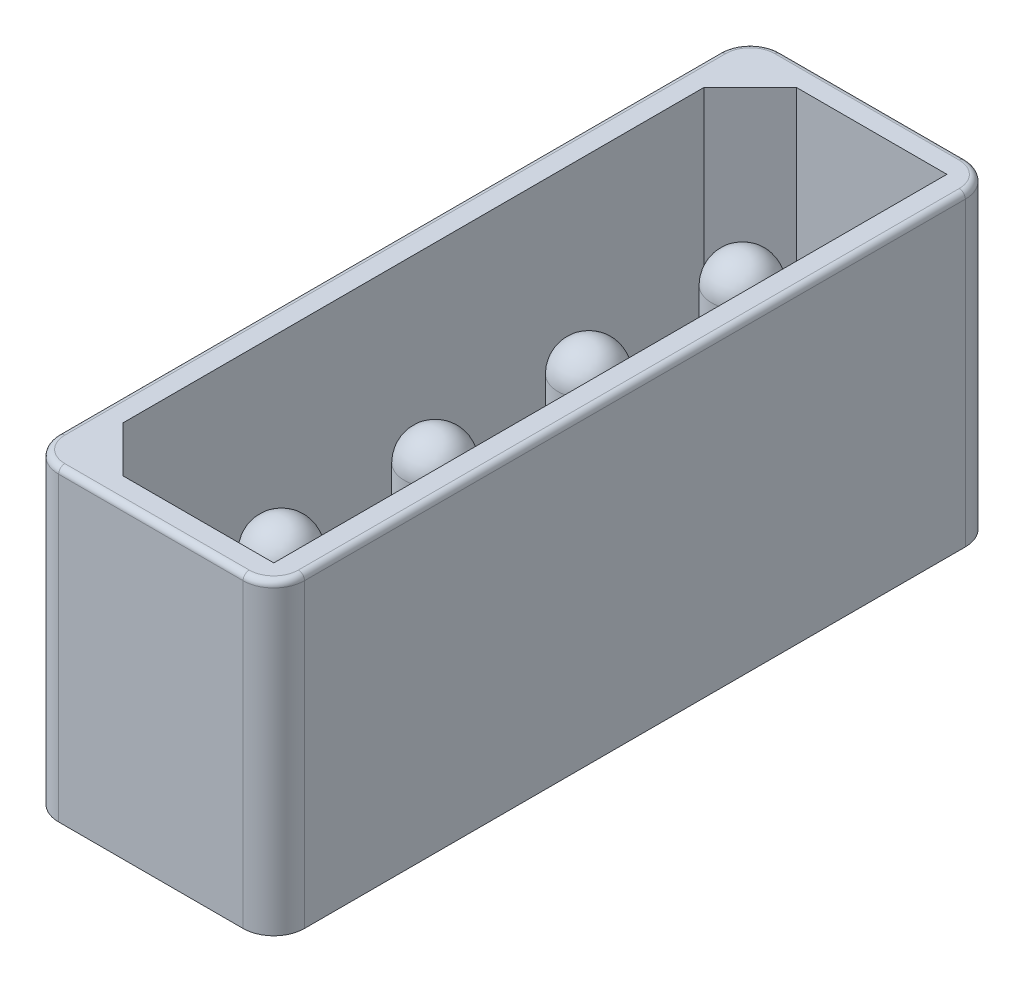
SolidWorks part; units mm, degrees
material "Duranickel(R) 301"
ref_plane "Alzado" through (0, 0, 0) normal (0, 0, 1) x (1, 0, 0)
ref_plane "Planta" through (0, 0, 0) normal (0, 1, 0) x (1, 0, 0)
ref_plane "Vista lateral" through (0, 0, 0) normal (1, 0, 0) x (0, 0, -1)
sketch "Croquis1" plane through (0, 0, 0) normal (0, 1, 0) x (1, 0, 0)
  line L0 (-3.2, 10.95) -> (-3.2, -10.95)
  line L1 (-4, 11.75) -> (4, 11.75)
  line L2 (-4, 11.75) -> (-4, -11.75)
  line L3 (-4, -11.75) -> (4, -11.75)
  line L4 (4, 11.75) -> (4, -11.75)
  line L5 (-3.2, -10.95) -> (3.2, -10.95)
  line L6 (3.2, 10.95) -> (3.2, -10.95)
  line L7 (-3.2, 10.95) -> (3.2, 10.95)
  dimension "D1" = 8
  dimension "D2" = 23.5
  dimension "D3" = 11.75
  dimension "D4" = 4
  dimension "D5" = 0.8
extrude "Extruir1" add sketch "Croquis1" along normal blind 11
chamfer "Chaflán1" distance 1.5 angle 45 2 edges at (-3.2, 5.5, 10.95) (-3.2, 5.5, -10.95)
fillet "Redondeo1" radius 1 4 edges at (-4, 5.5, 11.75) (4, 5.5, 11.75) (4, 5.5, -11.75) (-4, 5.5, -11.75)
fillet "Redondeo2" radius 0.2 8 edges at (-3.7071, 11, 11.4571) (-4, 11, 0) (-3.7071, 11, -11.4571) (0, 11, -11.75) (3.7071, 11, -11.4571) (4, 11, 0) (3.7071, 11, 11.4571) (0, 11, 11.75)
sketch "Croquis2" plane through (0, 0, 0) normal (0, -1, 0) x (1, 0, 0)
  line L4 (3, 11.75) -> (-3, 11.75)
  line L5 (-4, 10.75) -> (-4, -10.75)
  line L6 (-3, -11.75) -> (3, -11.75)
  line L7 (4, -10.75) -> (4, 10.75)
  line L8 (3, 11.75) -> (-3, 11.75)
  line L9 (-4, 10.75) -> (-4, -10.75)
  line L10 (-3, -11.75) -> (3, -11.75)
  line L11 (4, -10.75) -> (4, 10.75)
  arc A4 (-3, 11.75) -> (-4, 10.75) centre (-3, 10.75) ccw
  arc A5 (-4, -10.75) -> (-3, -11.75) centre (-3, -10.75) ccw
  arc A6 (3, -11.75) -> (4, -10.75) centre (3, -10.75) ccw
  arc A7 (4, 10.75) -> (3, 11.75) centre (3, 10.75) ccw
  arc A8 (-3, 11.75) -> (-4, 10.75) centre (-3, 10.75) ccw
  arc A9 (-4, -10.75) -> (-3, -11.75) centre (-3, -10.75) ccw
  arc A10 (3, -11.75) -> (4, -10.75) centre (3, -10.75) ccw
  arc A11 (4, 10.75) -> (3, 11.75) centre (3, 10.75) ccw
  dimension "D1" = 0
extrude "Extruir2" add sketch "Croquis2" against normal blind 1
sketch "Croquis3" plane through (0, 1, 0) normal (0, 1, 0) x (-1, 0, 0)
  circle A0 centre (0, 7.5) radius 1
  circle A1 centre (0, 2.5) radius 1
  circle A2 centre (0, -2.5) radius 1
  circle A3 centre (0, -7.5) radius 1
  dimension "D1" = 2
  dimension "D2" = 7.5
extrude "Extruir4" add sketch "Croquis3" along normal blind 8 separate body
fillet "Redondeo3" radius 1 1 edges at (0, 9, -6.5)
fillet "Redondeo4" radius 1 1 edges at (0, 9, -1.5)
fillet "Redondeo5" radius 1 1 edges at (0, 9, 3.5)
fillet "Redondeo6" radius 1 1 edges at (0, 9, 8.5)
sketch "Croquis4" plane through (-4, 0, 0) normal (-1, 0, 0) x (0, 0, 1)
  line L0 (-10.75, 0) -> (10.75, 0) construction
  line L1 (-12.4286, 1) -> (12.3548, 1)
  line L2 (-12.4286, 1) -> (-12.4286, -0.4014)
  line L3 (-12.4286, -0.4014) -> (12.3548, -0.4014)
  line L4 (12.3548, 1) -> (12.3548, -0.4014)
  dimension "D1" = 1
extrude "Cortar-Extruir1" cut sketch "Croquis4" against normal blind 14
sketch "Croquis5" plane through (0, 1, 0) normal (0, -1, 0) x (1, 0, 0)
  line L4 (-4, 10.75) -> (-4, -10.75)
  line L5 (-3, -11.75) -> (3, -11.75)
  line L6 (4, -10.75) -> (4, 10.75)
  line L7 (3, 11.75) -> (-3, 11.75)
  line L8 (-4, 10.75) -> (-4, -10.75)
  line L9 (-3, -11.75) -> (3, -11.75)
  line L10 (4, -10.75) -> (4, 10.75)
  line L11 (3, 11.75) -> (-3, 11.75)
  arc A4 (-3, 11.75) -> (-4, 10.75) centre (-3, 10.75) ccw
  arc A5 (-4, -10.75) -> (-3, -11.75) centre (-3, -10.75) ccw
  arc A6 (3, -11.75) -> (4, -10.75) centre (3, -10.75) ccw
  arc A7 (4, 10.75) -> (3, 11.75) centre (3, 10.75) ccw
  arc A8 (-3, 11.75) -> (-4, 10.75) centre (-3, 10.75) ccw
  arc A9 (-4, -10.75) -> (-3, -11.75) centre (-3, -10.75) ccw
  arc A10 (3, -11.75) -> (4, -10.75) centre (3, -10.75) ccw
  arc A11 (4, 10.75) -> (3, 11.75) centre (3, 10.75) ccw
  dimension "D1" = 0
extrude "Extruir5" add sketch "Croquis5" against normal blind 0.5 separate body
combine bodies "Combinar1" operation type add bodies to combine 109 108
